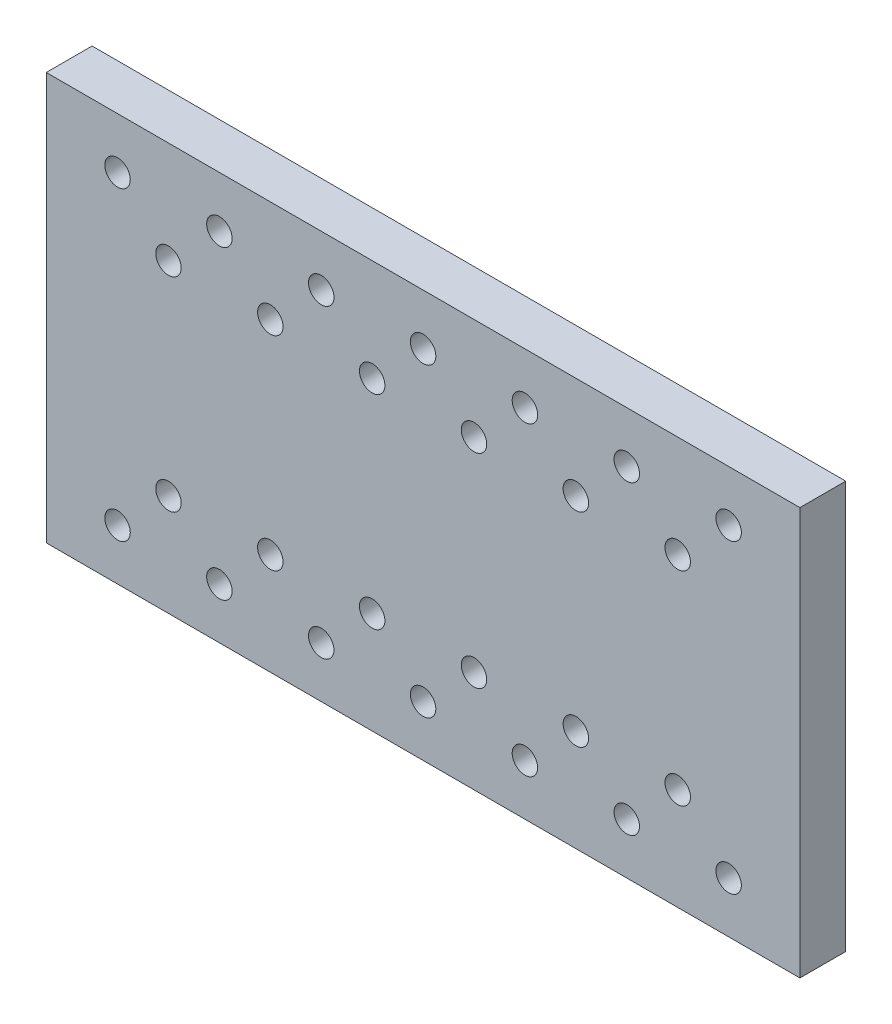
SolidWorks part; units mm, degrees
ref_plane "Front Plane" through (0, 0, 0) normal (0, 0, 1) x (1, 0, 0)
ref_plane "Top Plane" through (0, 0, 0) normal (0, 1, 0) x (1, 0, 0)
ref_plane "Right Plane" through (0, 0, 0) normal (1, 0, 0) x (0, 0, -1)
sketch "Sketch1" plane through (0, 0, 0) normal (0, 0, 1) x (1, 0, 0)
  line L0 (-194.093, 12.7) -> (0, 12.7) construction
  line L1 (0, 0) -> (-187.96, 0)
  line L2 (0, 0) -> (0, 101.6)
  line L3 (0, 101.6) -> (-187.96, 101.6)
  line L4 (-187.96, 0) -> (-187.96, 101.6)
  line L5 (-146.0159, 88.9) -> (0, 88.9) construction
  line L6 (-187.96, 25.4) -> (0, 25.4) construction
  line L7 (-187.96, 76.2) -> (0, 76.2) construction
  line L8 (-187.96, 50.8) -> (0, 50.8) construction
  line L9 (-93.98, 101.6) -> (-93.98, 0) construction
  circle A0 centre (-17.78, 88.9) radius 3.175
  circle A1 centre (-17.78, 12.7) radius 3.175
  circle A2 centre (-43.18, 12.7) radius 3.175
  circle A3 centre (-43.18, 88.9) radius 3.175
  circle A4 centre (-170.18, 88.9) radius 3.175
  circle A5 centre (-170.18, 12.7) radius 3.175
  circle A6 centre (-144.78, 12.7) radius 3.175
  circle A7 centre (-144.78, 88.9) radius 3.175
  circle A8 centre (-119.38, 88.9) radius 3.175
  circle A9 centre (-68.58, 88.9) radius 3.175
  circle A10 centre (-119.38, 12.7) radius 3.175
  circle A11 centre (-68.58, 12.7) radius 3.175
  circle A12 centre (-93.98, 88.9) radius 3.175
  circle A13 centre (-93.98, 12.7) radius 3.175
  circle A14 centre (-106.68, 76.2) radius 3.175
  circle A15 centre (-132.08, 76.2) radius 3.175
  circle A16 centre (-157.48, 76.2) radius 3.175
  circle A17 centre (-106.68, 25.4) radius 3.175
  circle A18 centre (-132.08, 25.4) radius 3.175
  circle A19 centre (-157.48, 25.4) radius 3.175
  circle A20 centre (-81.28, 76.2) radius 3.175
  circle A21 centre (-55.88, 76.2) radius 3.175
  circle A22 centre (-30.48, 76.2) radius 3.175
  circle A23 centre (-81.28, 25.4) radius 3.175
  circle A24 centre (-55.88, 25.4) radius 3.175
  circle A25 centre (-30.48, 25.4) radius 3.175
  dimension "D2" = 6.35
  dimension "D3" = 6.35
  dimension "D4" = 12.7
  dimension "D5" = 76.2
  dimension "D6" = 25.4
  dimension "D8" = 17.78
  dimension "D11" = 25.4
  dimension "D13" = 25.4
  dimension "D14" = 6.35
  dimension "D15" = 6.35
  dimension "D16" = 6.35
  dimension "D17" = 25.4
  dimension "D18" = 50.8
  dimension "D10" = 25.4
  dimension "D12" = 17.78
  dimension "D19" = 17.78
  dimension "D20" = 25.4
  dimension "D21" = 25.4
  dimension "D22" = 25.4
  dimension "D24" = 6.35
  dimension "D25" = 6.35
  dimension "D26" = 12.7
  dimension "D27" = 25.4
  dimension "D28" = 25.4
  dimension "D29" = 25.4
  dimension "D30" = 25.4
  dimension "D31" = 25.4
  dimension "D32" = 12.7
  dimension "D33" = 25.4
  dimension "D34" = 25.4
  dimension "D35" = 25.4
  dimension "D36" = 25.4
  dimension "D37" = 25.4
  dimension "D1" = 101.6
  dimension "D7" = 17.78
  dimension "D9" = 25.4
  dimension "D23" = 25.4
extrude "Boss-Extrude1" add sketch "Sketch1" along normal blind 11.43
